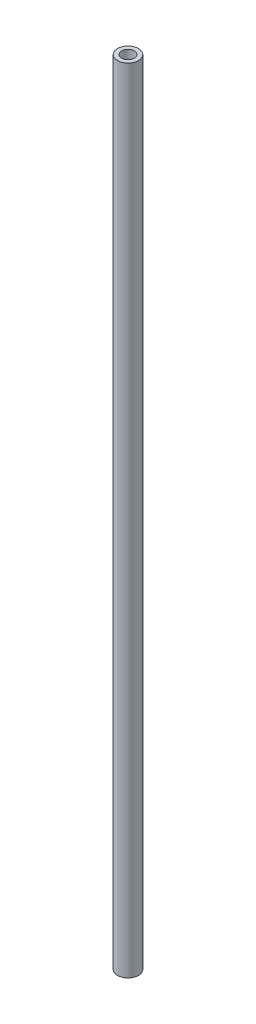
SolidWorks part; units mm, degrees
ref_plane "Front Plane" through (0, 0, 0) normal (0, 0, 1) x (1, 0, 0)
ref_plane "Top Plane" through (0, 0, 0) normal (0, 1, 0) x (1, 0, 0)
ref_plane "Right Plane" through (0, 0, 0) normal (1, 0, 0) x (0, 0, -1)
sketch "Sketch1" plane through (0, 0, 0) normal (0, 1, 0) x (1, 0, 0)
  circle A0 centre (0, 0) radius 4.0259
  circle A1 centre (0, 0) radius 2.4384
  dimension "D2" = 8.0518
  dimension "D1" = 1.5875
extrude "Boss-Extrude1" add sketch "Sketch1" along normal blind 304.8
equation "\"Socket Depth\"\t= 1.5in'Depth of Sockets in part"
equation "\"Roof Angle\"\t= 15deg'Angle of spoke to roof"
equation "\"Spoke Diameter\"= .317in'Diameter of spoke"
equation "\"Part Thickness\"= .125in'Thickness of injection-molded walls"
equation "\"Spoke Length\"\t= 8in'Length of spokes"
equation "\"D2@Sketch1\"= \"Spoke Diameter\""
equation "\"D1@Boss-Extrude1\" = \"Spoke Length2\""
equation "\"Spoke Length2\"\t= 12in'length of spokes"
equation "\"Center Spoke\"\t= 16in' lenth of center spoke"
